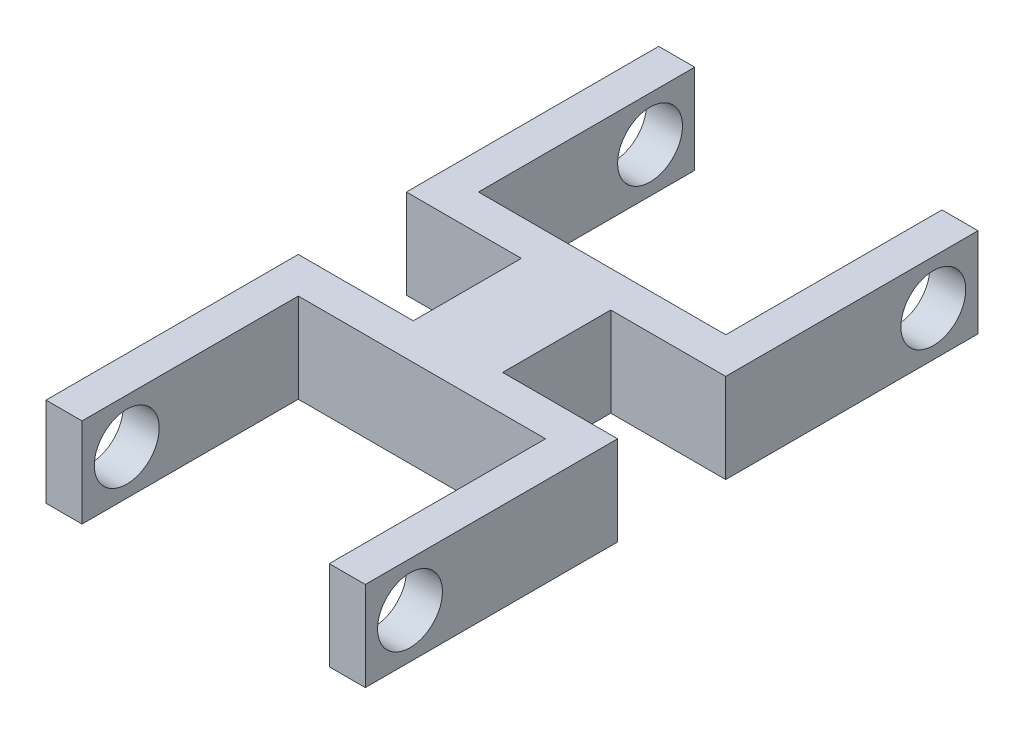
SolidWorks part; units mm, degrees
ref_plane "Front Plane" through (0, 0, 0) normal (0, 0, 1) x (1, 0, 0)
ref_plane "Top Plane" through (0, 0, 0) normal (0, 1, 0) x (1, 0, 0)
ref_plane "Right Plane" through (0, 0, 0) normal (1, 0, 0) x (0, 0, -1)
sketch "Sketch1" plane through (0, 0, 0) normal (0, 0, 1) x (1, 0, 0)
  line L1 (-22.15, 6.2) -> (22.15, 6.2)
  line L2 (-22.15, 6.2) -> (-22.15, -6.2)
  line L3 (-22.15, -6.2) -> (22.15, -6.2)
  line L4 (22.15, 6.2) -> (22.15, -6.2)
  line L5 (-22.15, 6.2) -> (22.15, -6.2) construction
  line L6 (-22.15, -6.2) -> (22.15, 6.2) construction
  point P0 (0, 0)
  dimension "D1" = 12.4
  dimension "D2" = 44.3
extrude "Boss-Extrude2" add sketch "Sketch1" along normal blind 5
sketch "Sketch2" plane through (0, 0, 5) normal (0, 0, 1) x (1, 0, 0)
  line L0 (-22.15, -6.2) -> (22.15, -6.2) construction
  line L1 (22.15, 6.2) -> (17.15, 6.2)
  line L2 (22.15, 6.2) -> (22.15, -6.2)
  line L3 (22.15, -6.2) -> (17.15, -6.2)
  line L4 (17.15, 6.2) -> (17.15, -6.2)
  line L6 (-22.15, 6.2) -> (-17.15, 6.2)
  line L7 (-22.15, 6.2) -> (-22.15, -6.2)
  line L8 (-22.15, -6.2) -> (-17.15, -6.2)
  line L9 (-17.15, 6.2) -> (-17.15, -6.2)
  dimension "D1" = 5
  dimension "D2" = 5
extrude "Boss-Extrude3" add sketch "Sketch2" along normal blind 30
sketch "Sketch3" plane through (22.15, 0, 0) normal (1, 0, 0) x (0, 0, -1)
  line L0 (-35, 6.2) -> (-35, -6.2) construction
  line L1 (-35, 0) -> (-28.8, 0) construction
  circle A0 centre (-28.8, 0) radius 4.5
  dimension "D1" = 6.2
extrude "Cut-Extrude1" cut sketch "Sketch3" against normal blind 50
sketch "Sketch5" plane through (0, 0, 0) normal (0, 0, -1) x (-1, 0, 0)
  line L0 (-22.15, 6.2) -> (22.15, 6.2) construction
  line L1 (-6.2, -6.2) -> (6.2, -6.2)
  line L2 (-6.2, -6.2) -> (-6.2, 6.2)
  line L3 (-6.2, 6.2) -> (6.2, 6.2)
  line L4 (6.2, -6.2) -> (6.2, 6.2)
  line L5 (-6.2, -6.2) -> (6.2, 6.2) construction
  line L6 (-6.2, 6.2) -> (6.2, -6.2) construction
  point P0 (0, 0)
  dimension "D1" = 12.4
extrude "Boss-Extrude5" add sketch "Sketch5" along normal blind 7.5
mirror "Mirror7" about plane through (0, 0, -7.5) normal (0, 0, 1) of "Boss-Extrude5", "Boss-Extrude3", "Boss-Extrude2", "Cut-Extrude1"
sketch "Sketch7" plane through (0, 0, -15) normal (0, 0, -1) x (-1, 0, 0)
  line L1 (-22.15, -6.2) -> (22.15, -6.2)
  line L2 (-22.15, -6.2) -> (-22.15, 6.2)
  line L3 (-22.15, 6.2) -> (22.15, 6.2)
  line L4 (22.15, -6.2) -> (22.15, 6.2)
  line L5 (-22.15, -6.2) -> (22.15, 6.2) construction
  line L6 (-22.15, 6.2) -> (22.15, -6.2) construction
  point P0 (0, 0)
  dimension "D1" = 44.3
  dimension "D2" = 12.4
extrude "Boss-Extrude6" add sketch "Sketch7" along normal blind 5
sketch "Sketch10" plane through (0, 0, -20) normal (0, 0, -1) x (-1, 0, 0)
  line L0 (-22.15, -6.2) -> (22.15, -6.2) construction
  line L1 (-22.15, 6.2) -> (-17.15, 6.2)
  line L2 (-22.15, 6.2) -> (-22.15, -6.2)
  line L3 (-22.15, -6.2) -> (-17.15, -6.2)
  line L4 (-17.15, 6.2) -> (-17.15, -6.2)
  line L6 (22.15, 6.2) -> (17.15, 6.2)
  line L7 (22.15, 6.2) -> (22.15, -6.2)
  line L8 (22.15, -6.2) -> (17.15, -6.2)
  line L9 (17.15, 6.2) -> (17.15, -6.2)
  dimension "D1" = 5
  dimension "D2" = 5
extrude "Boss-Extrude7" add sketch "Sketch10" along normal blind 30
sketch "Sketch11" plane through (-22.15, 0, 0) normal (-1, 0, 0) x (0, 0, 1)
  line L0 (-50, 0) -> (-43.8, 0) construction
  line L1 (-50, -6.2) -> (-50, 6.2) construction
  circle A0 centre (-43.8, 0) radius 4.5
  dimension "D1" = 6.2
extrude "Cut-Extrude2" cut sketch "Sketch11" against normal blind 50
